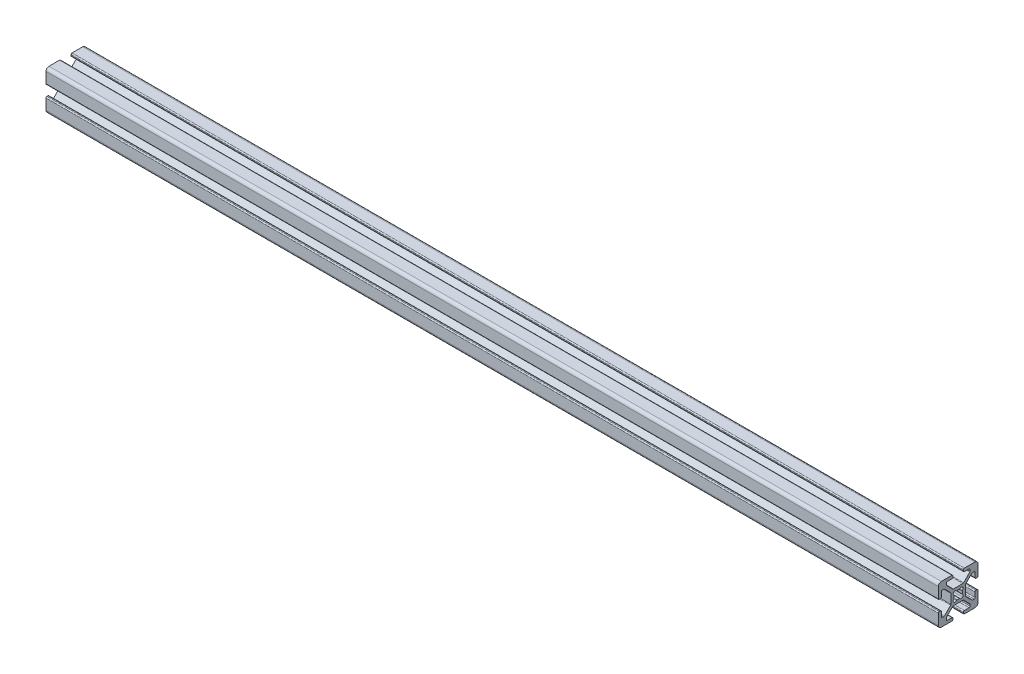
SolidWorks part; units mm, degrees
ref_plane "Front Plane" through (0, 0, 0) normal (0, 0, 1) x (1, 0, 0)
ref_plane "Top Plane" through (0, 0, 0) normal (0, 1, 0) x (1, 0, 0)
ref_plane "Right Plane" through (0, 0, 0) normal (1, 0, 0) x (0, 0, -1)
sketch "Sketch1" plane through (0, 0, 0) normal (0, 0, 1) x (1, 0, 0)
  line L0 (0, 0) -> (450, 0)
  dimension "D1" = 450
other "20_series 20-2020(1)"
ref_plane "Plane1" through (0, 0, 0) normal (1, 0, 0) x (0, 1, 0)
sketch "Sketch11" plane through (0, 0, 0) normal (1, 0, 0) x (0, 1, 0)
  line L0 (9.0094, 2.6289) -> (9.492, 2.6289)
  line L1 (8.5014, 5.4864) -> (8.5014, 3.1369)
  line L2 (10, 8.5014) -> (10, 3.1369)
  line L3 (7.2645, 5.9944) -> (7.9934, 5.9944)
  line L4 (3.1369, 10) -> (8.5014, 10)
  line L5 (3.8074, 2.7477) -> (6.9053, 5.8456)
  line L6 (2.6289, 9.0094) -> (2.6289, 9.492)
  line L7 (3.6586, -2.3885) -> (3.6586, 2.3885)
  line L8 (3.1369, 8.5014) -> (5.4864, 8.5014)
  line L9 (6.9053, -5.8456) -> (3.8074, -2.7477)
  line L10 (5.9944, 7.9934) -> (5.9944, 7.2645)
  line L11 (7.9934, -5.9944) -> (7.2645, -5.9944)
  line L12 (5.8456, 6.9053) -> (2.7477, 3.8074)
  line L13 (8.5014, -3.1369) -> (8.5014, -5.4864)
  line L14 (2.3885, 3.6586) -> (-2.3885, 3.6586)
  line L15 (9.0094, -2.6289) -> (9.492, -2.6289)
  line L16 (-2.7477, 3.8074) -> (-5.8456, 6.9053)
  line L17 (10, -3.1369) -> (10, -8.5014)
  line L18 (-5.9944, 7.2645) -> (-5.9944, 7.9934)
  line L19 (8.5014, -10) -> (3.1369, -10)
  line L20 (-5.4864, 8.5014) -> (-3.1369, 8.5014)
  line L21 (2.6289, -9.0094) -> (2.6289, -9.492)
  line L22 (-2.6289, 9.0094) -> (-2.6289, 9.492)
  line L23 (5.4864, -8.5014) -> (3.1369, -8.5014)
  line L24 (-8.5014, 10) -> (-3.1369, 10)
  line L25 (5.9944, -7.2645) -> (5.9944, -7.9934)
  line L26 (-10, 3.1369) -> (-10, 8.5014)
  line L27 (2.7477, -3.8074) -> (5.8456, -6.9053)
  line L28 (-9.0094, 2.6289) -> (-9.492, 2.6289)
  line L29 (-2.3885, -3.6586) -> (2.3885, -3.6586)
  line L30 (-8.5014, 3.1369) -> (-8.5014, 5.4864)
  line L31 (-5.8456, -6.9053) -> (-2.7477, -3.8074)
  line L32 (-7.9934, 5.9944) -> (-7.2645, 5.9944)
  line L33 (-5.9944, -7.9934) -> (-5.9944, -7.2645)
  line L34 (-6.9053, 5.8456) -> (-3.8074, 2.7477)
  line L35 (-3.1369, -8.5014) -> (-5.4864, -8.5014)
  line L36 (-3.6586, 2.3885) -> (-3.6586, -2.3885)
  line L37 (-2.6289, -9.0094) -> (-2.6289, -9.492)
  line L38 (-3.8074, -2.7477) -> (-6.9053, -5.8456)
  line L39 (-3.1369, -10) -> (-8.5014, -10)
  line L40 (-7.2645, -5.9944) -> (-7.9934, -5.9944)
  line L41 (-10, -8.5014) -> (-10, -3.1369)
  line L42 (-8.5014, -5.4864) -> (-8.5014, -3.1369)
  line L43 (-9.0094, -2.6289) -> (-9.492, -2.6289)
  line L44 (-2.2966, 2.1217) -> (-2.1217, 2.2966)
  line L45 (2.1217, 2.2966) -> (2.2966, 2.1217)
  line L46 (-2.1217, -2.2966) -> (-2.2966, -2.1217)
  line L47 (2.2966, -2.1217) -> (2.1217, -2.2966)
  arc A0 (8.5014, 3.1369) -> (9.0094, 2.6289) centre (9.0094, 3.1369) ccw
  arc A1 (9.492, 2.6289) -> (10, 3.1369) centre (9.492, 3.1369) ccw
  arc A2 (8.5014, 5.4864) -> (7.9934, 5.9944) centre (7.9934, 5.4864) ccw
  arc A3 (10, 8.5014) -> (8.5014, 10) centre (8.5014, 8.5014) ccw
  arc A4 (7.2645, 5.9944) -> (6.9053, 5.8456) centre (7.2645, 5.4864) ccw
  arc A5 (3.1369, 10) -> (2.6289, 9.492) centre (3.1369, 9.492) ccw
  arc A6 (3.8074, 2.7477) -> (3.6586, 2.3885) centre (4.1666, 2.3885) ccw
  arc A7 (2.6289, 9.0094) -> (3.1369, 8.5014) centre (3.1369, 9.0094) ccw
  arc A8 (3.6586, -2.3885) -> (3.8074, -2.7477) centre (4.1666, -2.3885) ccw
  arc A9 (5.9944, 7.9934) -> (5.4864, 8.5014) centre (5.4864, 7.9934) ccw
  arc A10 (6.9053, -5.8456) -> (7.2645, -5.9944) centre (7.2645, -5.4864) ccw
  arc A11 (5.8456, 6.9053) -> (5.9944, 7.2645) centre (5.4864, 7.2645) ccw
  arc A12 (7.9934, -5.9944) -> (8.5014, -5.4864) centre (7.9934, -5.4864) ccw
  arc A13 (2.3885, 3.6586) -> (2.7477, 3.8074) centre (2.3885, 4.1666) ccw
  arc A14 (9.0094, -2.6289) -> (8.5014, -3.1369) centre (9.0094, -3.1369) ccw
  arc A15 (-2.7477, 3.8074) -> (-2.3885, 3.6586) centre (-2.3885, 4.1666) ccw
  arc A16 (10, -3.1369) -> (9.492, -2.6289) centre (9.492, -3.1369) ccw
  arc A17 (-5.9944, 7.2645) -> (-5.8456, 6.9053) centre (-5.4864, 7.2645) ccw
  arc A18 (8.5014, -10) -> (10, -8.5014) centre (8.5014, -8.5014) ccw
  arc A19 (-5.4864, 8.5014) -> (-5.9944, 7.9934) centre (-5.4864, 7.9934) ccw
  arc A20 (2.6289, -9.492) -> (3.1369, -10) centre (3.1369, -9.492) ccw
  arc A21 (-3.1369, 8.5014) -> (-2.6289, 9.0094) centre (-3.1369, 9.0094) ccw
  arc A22 (3.1369, -8.5014) -> (2.6289, -9.0094) centre (3.1369, -9.0094) ccw
  arc A23 (-2.6289, 9.492) -> (-3.1369, 10) centre (-3.1369, 9.492) ccw
  arc A24 (5.4864, -8.5014) -> (5.9944, -7.9934) centre (5.4864, -7.9934) ccw
  arc A25 (-8.5014, 10) -> (-10, 8.5014) centre (-8.5014, 8.5014) ccw
  arc A26 (5.9944, -7.2645) -> (5.8456, -6.9053) centre (5.4864, -7.2645) ccw
  arc A27 (-10, 3.1369) -> (-9.492, 2.6289) centre (-9.492, 3.1369) ccw
  arc A28 (2.7477, -3.8074) -> (2.3885, -3.6586) centre (2.3885, -4.1666) ccw
  arc A29 (-9.0094, 2.6289) -> (-8.5014, 3.1369) centre (-9.0094, 3.1369) ccw
  arc A30 (-2.3885, -3.6586) -> (-2.7477, -3.8074) centre (-2.3885, -4.1666) ccw
  arc A31 (-7.9934, 5.9944) -> (-8.5014, 5.4864) centre (-7.9934, 5.4864) ccw
  arc A32 (-5.8456, -6.9053) -> (-5.9944, -7.2645) centre (-5.4864, -7.2645) ccw
  arc A33 (-6.9053, 5.8456) -> (-7.2645, 5.9944) centre (-7.2645, 5.4864) ccw
  arc A34 (-5.9944, -7.9934) -> (-5.4864, -8.5014) centre (-5.4864, -7.9934) ccw
  arc A35 (-3.6586, 2.3885) -> (-3.8074, 2.7477) centre (-4.1666, 2.3885) ccw
  arc A36 (-2.6289, -9.0094) -> (-3.1369, -8.5014) centre (-3.1369, -9.0094) ccw
  arc A37 (-3.8074, -2.7477) -> (-3.6586, -2.3885) centre (-4.1666, -2.3885) ccw
  arc A38 (-3.1369, -10) -> (-2.6289, -9.492) centre (-3.1369, -9.492) ccw
  arc A39 (-7.2645, -5.9944) -> (-6.9053, -5.8456) centre (-7.2645, -5.4864) ccw
  arc A40 (-10, -8.5014) -> (-8.5014, -10) centre (-8.5014, -8.5014) ccw
  arc A41 (-8.5014, -5.4864) -> (-7.9934, -5.9944) centre (-7.9934, -5.4864) ccw
  arc A42 (-9.492, -2.6289) -> (-10, -3.1369) centre (-9.492, -3.1369) ccw
  arc A43 (-8.5014, -3.1369) -> (-9.0094, -2.6289) centre (-9.0094, -3.1369) ccw
  arc A44 (-0.8806, 2.1293) -> (-0.5885, 2.0112) centre (-0.6599, 2.2549) ccw
  arc A45 (0.5885, 2.0112) -> (-0.5885, 2.0112) centre (0, 0) ccw
  arc A46 (-0.8806, 2.1293) -> (-2.1217, 2.2966) centre (-1.565, 1.7398) ccw
  arc A47 (0.5885, 2.0112) -> (0.8806, 2.1293) centre (0.6599, 2.2549) ccw
  arc A48 (2.1217, 2.2966) -> (0.8806, 2.1293) centre (1.565, 1.7398) ccw
  arc A49 (-2.2966, 2.1217) -> (-2.1293, 0.8806) centre (-1.7398, 1.565) ccw
  arc A50 (-2.0112, 0.5885) -> (-2.1293, 0.8806) centre (-2.2549, 0.6599) ccw
  arc A51 (2.1293, 0.8806) -> (2.2966, 2.1217) centre (1.7398, 1.565) ccw
  arc A52 (-2.0112, 0.5885) -> (-2.0112, -0.5885) centre (0, 0) ccw
  arc A53 (2.1293, 0.8806) -> (2.0112, 0.5885) centre (2.2549, 0.6599) ccw
  arc A54 (-2.1293, -0.8806) -> (-2.0112, -0.5885) centre (-2.2549, -0.6599) ccw
  arc A55 (2.0112, -0.5885) -> (2.0112, 0.5885) centre (0, 0) ccw
  arc A56 (-2.1293, -0.8806) -> (-2.2966, -2.1217) centre (-1.7398, -1.565) ccw
  arc A57 (2.0112, -0.5885) -> (2.1293, -0.8806) centre (2.2549, -0.6599) ccw
  arc A58 (2.2966, -2.1217) -> (2.1293, -0.8806) centre (1.7398, -1.565) ccw
  arc A59 (-2.1217, -2.2966) -> (-0.8806, -2.1293) centre (-1.565, -1.7398) ccw
  arc A60 (-0.5885, -2.0112) -> (-0.8806, -2.1293) centre (-0.6599, -2.2549) ccw
  arc A61 (0.8806, -2.1293) -> (2.1217, -2.2966) centre (1.565, -1.7398) ccw
  arc A62 (-0.5885, -2.0112) -> (0.5885, -2.0112) centre (0, 0) ccw
  arc A63 (0.8806, -2.1293) -> (0.5885, -2.0112) centre (0.6599, -2.2549) ccw
  point P0 (0, 0)
